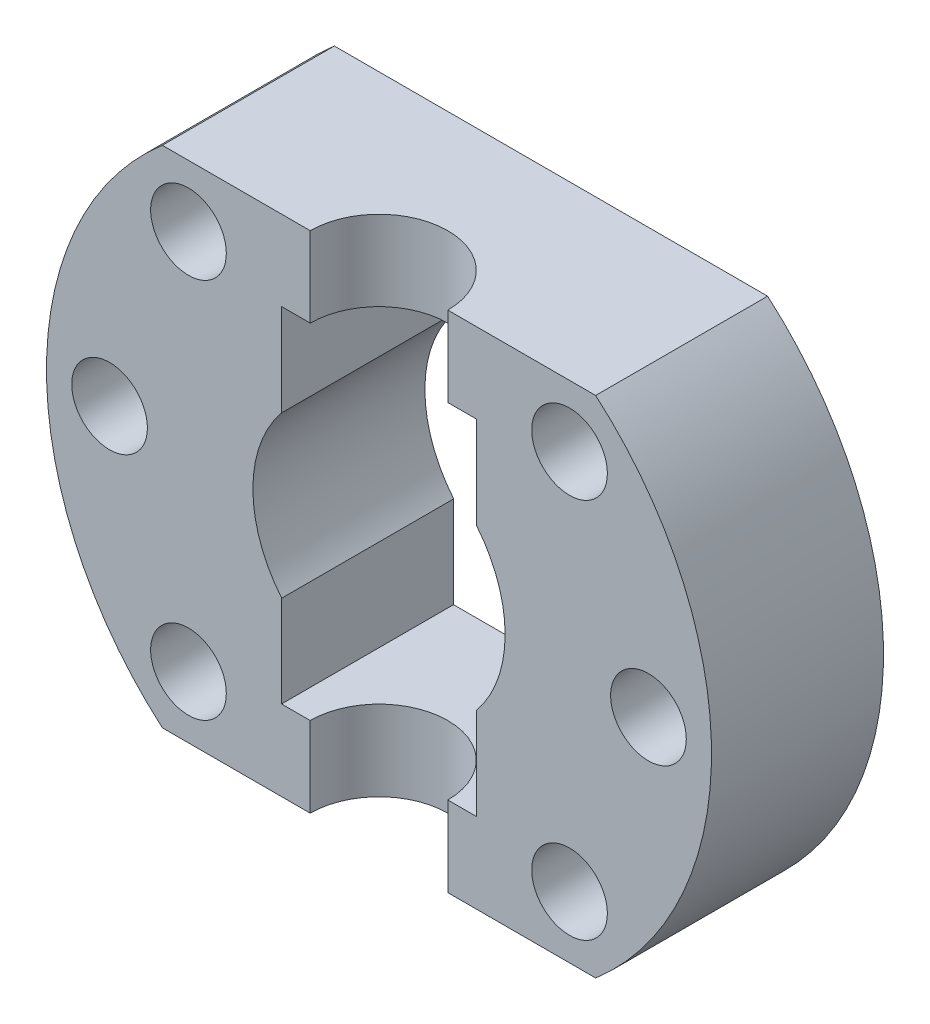
SolidWorks part; units mm, degrees
ref_plane "Płaszczyzna przednia" through (0, 0, 0) normal (0, 0, 1) x (1, 0, 0)
ref_plane "Płaszczyzna górna" through (0, 0, 0) normal (0, 1, 0) x (1, 0, 0)
ref_plane "Płaszczyzna prawa" through (0, 0, 0) normal (1, 0, 0) x (0, 0, -1)
sketch "Szkic1" plane through (0, 0, 0) normal (0, 0, 1) x (1, 0, 0)
  line L0 (0, 0) -> (0, 22) construction
  line L1 (-18.8944, 22) -> (18.8944, 22)
  line L2 (-29, 0) -> (29, 0) construction
  line L3 (-18.8944, -22) -> (18.8944, -22)
  arc A0 (-18.8944, 22) -> (-18.8944, -22) centre (0, 0) ccw
  arc A1 (18.8944, -22) -> (18.8944, 22) centre (0, 0) ccw
  circle A2 centre (0, 0) radius 23.5 construction
  circle A3 centre (-23.5, 0) radius 3.3
  circle A4 centre (-16.617, 16.617) radius 3.3
  circle A5 centre (0, 23.5) radius 3.3 [skipped]
  circle A6 centre (16.617, 16.617) radius 3.3
  circle A7 centre (23.5, 0) radius 3.3
  circle A8 centre (16.617, -16.617) radius 3.3
  circle A9 centre (0, -23.5) radius 3.3 [skipped]
  circle A10 centre (-16.617, -16.617) radius 3.3
  circle A11 centre (0, 0) radius 11
  point P29 (0, 0)
  dimension "D1" = 29
  dimension "D3" = 8
  dimension "D4" = 6.6
  dimension "D5" = 47
  dimension "D6" = 22
  dimension "D2" = 22
extrude "Dodanie-wyciągnięcie2" add sketch "Szkic1" along normal blind 15
sketch "Szkic2" plane through (0, 0, 15) normal (0, 0, 1) x (1, 0, 0)
  line L0 (0, 0) -> (0, -11)
  line L1 (0, 0) -> (0, 11)
  line L2 (-8.5, -7) -> (8.5, -7)
  line L3 (-8.5, -7) -> (-8.5, -15)
  line L4 (-8.5, -15) -> (8.5, -15)
  line L5 (8.5, -7) -> (8.5, -15)
  line L6 (-8.5, -7) -> (8.5, -15) construction
  line L7 (-8.5, -15) -> (8.5, -7) construction
  line L9 (-8.5, 15.0179) -> (8.5, 15.0179)
  line L10 (-8.5, 15.0179) -> (-8.5, 6.9821)
  line L11 (-8.5, 6.9821) -> (8.5, 6.9821)
  line L12 (8.5, 15.0179) -> (8.5, 6.9821)
  line L13 (-8.5, 15.0179) -> (8.5, 6.9821) construction
  line L14 (-8.5, 6.9821) -> (8.5, 15.0179) construction
  circle A0 centre (0, 0) radius 11 construction
  dimension "D1" = 8
  dimension "D2" = 17
extrude "Wytnij-wyciągnięcie1" cut sketch "Szkic2" against normal through all contours L2 L5 L4 L3 | L11 L12 L9 L10
sketch "Szkic3" plane through (0, -22, 0) normal (0, -1, 0) x (1, 0, 0)
  line L0 (-18.8944, 15) -> (18.8944, 15) construction
  circle A0 centre (0, 15) radius 6
  dimension "D1" = 12
extrude "Wytnij-wyciągnięcie2" cut sketch "Szkic3" against normal through all
